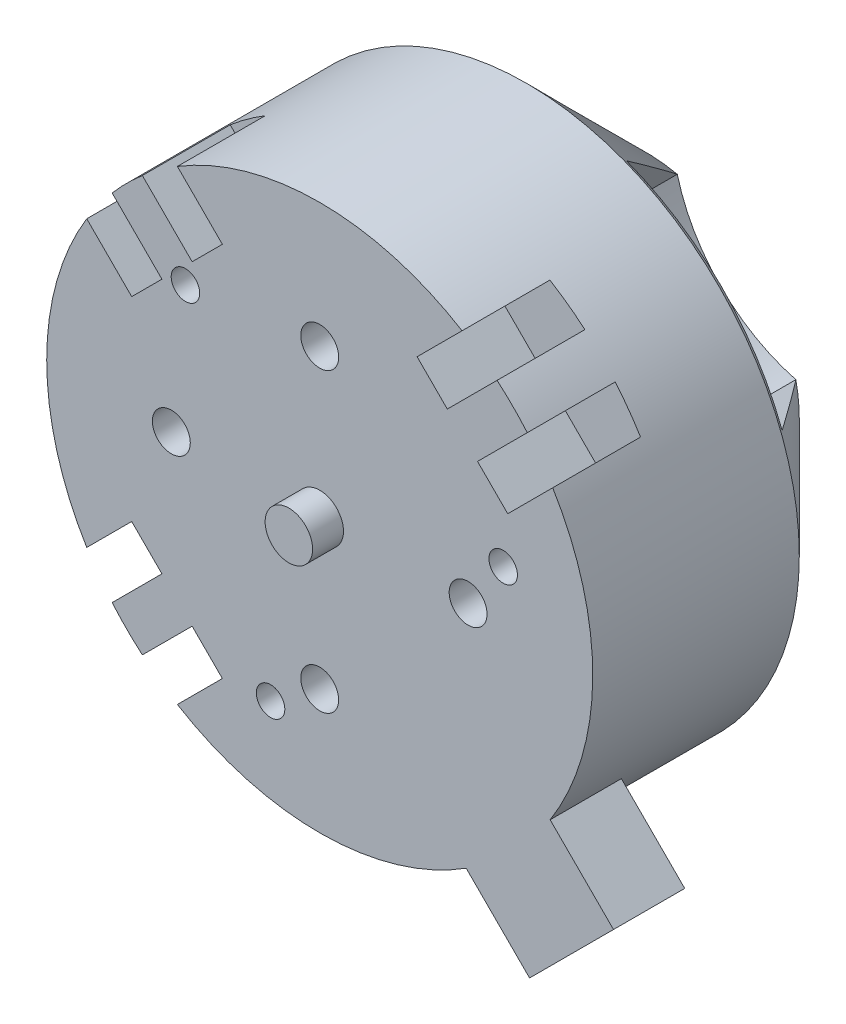
SolidWorks part; units mm, degrees
ref_plane "前视基准面" through (0, 0, 0) normal (0, 0, 1) x (1, 0, 0)
ref_plane "上视基准面" through (0, 0, 0) normal (0, 1, 0) x (1, 0, 0)
ref_plane "右视基准面" through (0, 0, 0) normal (1, 0, 0) x (0, 0, -1)
sketch "草图1" plane through (0, 0, 0) normal (0, 0, 1) x (1, 0, 0)
  circle A0 centre (0, 0) radius 23
extrude "凸台-拉伸1" add sketch "草图1" along normal blind 25
sketch "草图2" plane through (0, 0, 0) normal (0, 0, -1) x (-1, 0, 0)
  circle A0 centre (6, 0) radius 1.5
  circle A1 centre (0, -6) radius 1.5
  circle A2 centre (-6, 0) radius 1.5
  circle A3 centre (0, 6) radius 1.5
  circle A4 centre (0, 0) radius 2.6
  point P10 (0, 0)
extrude "切除-拉伸1" cut sketch "草图2" against normal blind 10
sketch "草图3" plane through (0, 0, 10) normal (0, 0, -1) x (-1, 0, 0)
  circle A1 centre (0, 0) radius 2.6
  circle A2 centre (0, 0) radius 2.6
  dimension "D1" = 0
extrude "凸台-拉伸2" add sketch "草图3" against normal offset from surface (27 mm away) 12 up to face at (23, 0, 25) offset beyond the face yes
chamfer "倒角1" distance 10 angle 45 1 edges at (23, 0, 0)
sketch "草图4" plane through (0, 0, 0) normal (0, 0, -1) x (-1, 0, 0)
  line L0 (2.7214, -12.712) -> (8.2046, -21.4869)
  line L1 (12.712, 2.7214) -> (21.4869, 8.2046)
  line L2 (2.7214, 12.712) -> (8.2046, 21.4869)
  line L3 (12.712, -2.7214) -> (21.4869, -8.2046)
  line L4 (-12.712, -2.7214) -> (-21.4869, -8.2046)
  line L5 (-2.7214, -12.712) -> (-8.2046, -21.4869)
  line L6 (-2.7214, 12.712) -> (-8.2046, 21.4869)
  line L7 (-12.712, 2.7214) -> (-21.4869, 8.2046)
  arc A0 (12.712, -2.7214) -> (2.7214, -12.712) centre (16.2635, -16.2635) ccw
  circle A1 centre (0, 0) radius 13 construction
  circle A2 centre (0, 0) radius 23 construction
  arc A3 (2.7214, 12.712) -> (12.712, 2.7214) centre (16.2635, 16.2635) ccw
  arc A4 (12.712, -2.7214) -> (-12.712, -2.7214) centre (0, 0) ccw
  arc A5 (21.4869, 8.2046) -> (8.2046, 21.4869) centre (0, 0) ccw
  arc A6 (12.712, -2.7214) -> (-12.712, -2.7214) centre (0, 0) ccw
  arc A7 (8.2046, -21.4869) -> (21.4869, -8.2046) centre (0, 0) ccw
  arc A8 (-2.7214, -12.712) -> (-12.712, -2.7214) centre (-16.2635, -16.2635) ccw
  arc A9 (12.712, -2.7214) -> (-12.712, -2.7214) centre (0, 0) ccw
  arc A10 (-21.4869, -8.2046) -> (-8.2046, -21.4869) centre (0, 0) ccw
  arc A11 (-12.712, 2.7214) -> (-2.7214, 12.712) centre (-16.2635, 16.2635) ccw
  arc A12 (12.712, -2.7214) -> (-12.712, -2.7214) centre (0, 0) ccw
  arc A13 (-8.2046, 21.4869) -> (-21.4869, 8.2046) centre (0, 0) ccw
  arc A14 (2.7214, -12.712) -> (3.8008, -12.432) centre (0, 0) ccw
  arc A15 (2.7214, -12.712) -> (3.8008, -12.432) centre (0, 0) ccw
  arc A16 (2.7214, -12.712) -> (3.8008, -12.432) centre (0, 0) ccw
  arc A17 (2.7214, -12.712) -> (3.8008, -12.432) centre (0, 0) ccw
  point P31 (0, 0)
  circle M12 centre (0, 0) radius 13
  dimension "D1" = 4
extrude "切除-拉伸2" cut sketch "草图4" against normal blind 9.5 contours L0 A7 L3 M12 | A0 M12 | A3 M12 | L1 A5 L2 M12 | L6 A13 L7 M12 | A11 M12 | L4 A10 L5 M12 | A8 M12
sketch "草图5" plane through (0, 0, 25) normal (0, 0, 1) x (1, 0, 0)
  circle A4 centre (0, 12.5) radius 1.5957
  circle A5 centre (12.5, 0) radius 1.5957
  circle A6 centre (0, -12.5) radius 1.5957
  circle A7 centre (-12.5, 0) radius 1.5957
  point P13 (-4.7872, 7.4468)
  point P15 (-4.7872, -7.4468)
  point P27 (0, 0)
  point P32 (0, 0)
  point P41 (0, 0)
extrude "切除-拉伸3" cut sketch "草图5" against normal blind 2
sketch "草图6" plane through (0, 0, 37) normal (0, 0, 1) x (1, 0, 0)
  circle A1 centre (0, 0) radius 2.6
  circle A2 centre (0, 0) radius 2.6
  dimension "D1" = 0
extrude "切除-拉伸4" cut sketch "草图6" against normal up to surface (12 mm away) up to face at (1.5957, 12.5, 25)
sketch "草图7" plane through (0, 0, 25) normal (0, 0, 1) x (1, 0, 0)
  circle A0 centre (0, 0) radius 2
extrude "凸台-拉伸3" add sketch "草图7" along normal blind 5
sketch "草图8" plane through (0, 0, 25) normal (0, 0, 1) x (1, 0, 0)
  line L1 (17.6777, -24.7487) -> (24.7487, -17.6777)
  line L2 (24.7487, -17.6777) -> (17.5976, -10.5265)
  line L3 (17.5976, -10.5265) -> (10.5265, -17.5976)
  line L4 (17.6777, -24.7487) -> (10.5265, -17.5976)
  point P7 (14.062, -14.062)
extrude "凸台-拉伸4" add sketch "草图8" against normal blind 5
sketch "草图9" plane through (0, 0, 25) normal (0, 0, 1) x (1, 0, 0)
  line L0 (10.748, 13.2936) -> (14.9408, 17.4864)
  line L1 (-13.2936, 10.748) -> (-17.4864, 14.9408)
  line L2 (-10.748, 13.2936) -> (-8.2024, 15.8392)
  line L3 (-10.748, 13.2936) -> (-14.7902, 17.3358)
  line L4 (-8.2024, 15.8392) -> (-10.748, 13.2936)
  line L5 (-8.2024, 15.8392) -> (-11.9905, 19.6272)
  line L6 (-15.8392, 8.2024) -> (-19.6272, 11.9905)
  line L7 (-8.2024, 15.8392) -> (-10.748, 13.2936)
  line L8 (-8.2024, 15.8392) -> (-11.9905, 19.6272)
  line L9 (-10.748, 13.2936) -> (-14.9408, 17.4864)
  line L10 (-15.8392, 8.2024) -> (-13.2936, 10.748)
  line L11 (-15.8392, 8.2024) -> (-19.6272, 11.9905)
  line L12 (-15.8392, 8.2024) -> (-13.2936, 10.748)
  line L13 (-13.2936, 10.748) -> (-17.3358, 14.7902)
  line L14 (-13.2936, 10.748) -> (-15.8392, 8.2024)
  line L15 (13.2936, 10.748) -> (15.8392, 8.2024)
  line L16 (13.2936, 10.748) -> (17.3358, 14.7902)
  line L17 (15.8392, 8.2024) -> (13.2936, 10.748)
  line L18 (15.8392, 8.2024) -> (19.6272, 11.9905)
  line L19 (8.2024, 15.8392) -> (11.9905, 19.6272)
  line L20 (15.8392, 8.2024) -> (13.2936, 10.748)
  line L21 (15.8392, 8.2024) -> (19.6272, 11.9905)
  line L22 (13.2936, 10.748) -> (17.4864, 14.9408)
  line L23 (8.2024, 15.8392) -> (10.748, 13.2936)
  line L24 (8.2024, 15.8392) -> (11.9905, 19.6272)
  line L25 (8.2024, 15.8392) -> (10.748, 13.2936)
  line L26 (10.748, 13.2936) -> (14.7902, 17.3358)
  line L27 (10.748, 13.2936) -> (8.2024, 15.8392)
  line L28 (-10.748, -13.2936) -> (-14.9408, -17.4864)
  line L29 (-13.2936, -10.748) -> (-15.8392, -8.2024)
  line L30 (-13.2936, -10.748) -> (-17.3358, -14.7902)
  line L31 (-15.8392, -8.2024) -> (-13.2936, -10.748)
  line L32 (-15.8392, -8.2024) -> (-19.6272, -11.9905)
  line L33 (-8.2024, -15.8392) -> (-11.9905, -19.6272)
  line L34 (-15.8392, -8.2024) -> (-13.2936, -10.748)
  line L35 (-15.8392, -8.2024) -> (-19.6272, -11.9905)
  line L36 (-13.2936, -10.748) -> (-17.4864, -14.9408)
  line L37 (-8.2024, -15.8392) -> (-10.748, -13.2936)
  line L38 (-8.2024, -15.8392) -> (-11.9905, -19.6272)
  line L39 (-8.2024, -15.8392) -> (-10.748, -13.2936)
  line L40 (-10.748, -13.2936) -> (-14.7902, -17.3358)
  line L41 (-10.748, -13.2936) -> (-8.2024, -15.8392)
  arc A1 (19.41, -12.339) -> (12.339, -19.41) centre (0, 0) ccw construction
  arc A2 (19.41, -12.339) -> (12.339, -19.41) centre (0, 0) ccw
  point P38 (0, 0)
  arc M1 (19.41, -12.339) -> (12.339, -19.41) centre (0, 0) ccw
extrude "切除-拉伸5" cut sketch "草图9" against normal blind 5 contours L6 L10 L1 M1 | L9 L3 L2 L5 M1 | L19 L23 L0 M1 | L22 L16 L15 L18 M1 | L33 L37 L28 M1 | L36 L30 L29 L32 M1
sketch "草图10" plane through (0, 0, 25) normal (0, 0, 1) x (1, 0, 0)
  line L21 (-10.748, -13.2936) -> (-8.2024, -15.8392)
  line L22 (-8.2024, -15.8392) -> (-11.9905, -19.6272)
  line L23 (12.339, -19.41) -> (17.6777, -24.7487)
  line L24 (17.6777, -24.7487) -> (24.7487, -17.6777)
  line L25 (24.7487, -17.6777) -> (19.41, -12.339)
  line L26 (19.6272, 11.9905) -> (15.8392, 8.2024)
  line L27 (15.8392, 8.2024) -> (13.2936, 10.748)
  line L28 (13.2936, 10.748) -> (17.4864, 14.9408)
  line L29 (14.9408, 17.4864) -> (10.748, 13.2936)
  line L30 (10.748, 13.2936) -> (8.2024, 15.8392)
  line L31 (8.2024, 15.8392) -> (11.9905, 19.6272)
  line L32 (-11.9905, 19.6272) -> (-8.2024, 15.8392)
  line L33 (-8.2024, 15.8392) -> (-10.748, 13.2936)
  line L34 (-10.748, 13.2936) -> (-14.9408, 17.4864)
  line L35 (-17.4864, 14.9408) -> (-13.2936, 10.748)
  line L36 (-13.2936, 10.748) -> (-15.8392, 8.2024)
  line L37 (-15.8392, 8.2024) -> (-19.6272, 11.9905)
  line L38 (-19.6272, -11.9905) -> (-15.8392, -8.2024)
  line L39 (-15.8392, -8.2024) -> (-13.2936, -10.748)
  line L40 (-13.2936, -10.748) -> (-17.4864, -14.9408)
  line L41 (-14.9408, -17.4864) -> (-10.748, -13.2936)
  line L42 (-10.748, -13.2936) -> (-8.2024, -15.8392)
  line L43 (-8.2024, -15.8392) -> (-11.9905, -19.6272)
  line L44 (12.339, -19.41) -> (17.6777, -24.7487)
  line L45 (17.6777, -24.7487) -> (24.7487, -17.6777)
  line L46 (24.7487, -17.6777) -> (19.41, -12.339)
  line L47 (19.6272, 11.9905) -> (15.8392, 8.2024)
  line L48 (15.8392, 8.2024) -> (13.2936, 10.748)
  line L49 (13.2936, 10.748) -> (17.4864, 14.9408)
  line L50 (14.9408, 17.4864) -> (10.748, 13.2936)
  line L51 (10.748, 13.2936) -> (8.2024, 15.8392)
  line L52 (8.2024, 15.8392) -> (11.9905, 19.6272)
  line L53 (-11.9905, 19.6272) -> (-8.2024, 15.8392)
  line L54 (-8.2024, 15.8392) -> (-10.748, 13.2936)
  line L55 (-10.748, 13.2936) -> (-14.9408, 17.4864)
  line L56 (-17.4864, 14.9408) -> (-13.2936, 10.748)
  line L57 (-13.2936, 10.748) -> (-15.8392, 8.2024)
  line L58 (-15.8392, 8.2024) -> (-19.6272, 11.9905)
  line L59 (-19.6272, -11.9905) -> (-15.8392, -8.2024)
  line L60 (-15.8392, -8.2024) -> (-13.2936, -10.748)
  line L61 (-13.2936, -10.748) -> (-17.4864, -14.9408)
  line L62 (-14.9408, -17.4864) -> (-10.748, -13.2936)
  circle A0 centre (0, 12.5) radius 1.5957 construction
  circle A1 centre (-12.5, 0) radius 1.5957 construction
  circle A2 centre (0, -12.5) radius 1.5957 construction
  circle A3 centre (12.5, 0) radius 1.5957 construction
  circle A4 centre (0, 12.5) radius 1.5957
  circle A5 centre (-12.5, 0) radius 1.5957
  circle A6 centre (0, -12.5) radius 1.5957
  arc A7 (-11.9905, -19.6272) -> (12.339, -19.41) centre (0, 0) ccw
  arc A8 (19.41, -12.339) -> (19.6272, 11.9905) centre (0, 0) ccw
  arc A9 (17.4864, 14.9408) -> (14.9408, 17.4864) centre (0, 0) ccw
  arc A10 (11.9905, 19.6272) -> (-11.9905, 19.6272) centre (0, 0) ccw
  arc A11 (-14.9408, 17.4864) -> (-17.4864, 14.9408) centre (0, 0) ccw
  arc A12 (-19.6272, 11.9905) -> (-19.6272, -11.9905) centre (0, 0) ccw
  arc A13 (-17.4864, -14.9408) -> (-14.9408, -17.4864) centre (0, 0) ccw
  arc A14 (-11.9905, -19.6272) -> (12.339, -19.41) centre (0, 0) ccw
  arc A15 (19.41, -12.339) -> (19.6272, 11.9905) centre (0, 0) ccw
  arc A16 (17.4864, 14.9408) -> (14.9408, 17.4864) centre (0, 0) ccw
  arc A17 (11.9905, 19.6272) -> (-11.9905, 19.6272) centre (0, 0) ccw
  arc A18 (-14.9408, 17.4864) -> (-17.4864, 14.9408) centre (0, 0) ccw
  arc A19 (-19.6272, 11.9905) -> (-19.6272, -11.9905) centre (0, 0) ccw
  arc A20 (-17.4864, -14.9408) -> (-14.9408, -17.4864) centre (0, 0) ccw
  circle A21 centre (12.5, 0) radius 1.5957
  dimension "D1" = 0
extrude "凸台-拉伸5" add sketch "草图10" along normal blind 2.4
sketch "草图11" plane through (0, 0, 20) normal (0, 0, -1) x (-1, 0, 0)
  line L3 (-17.6777, -24.7487) -> (-12.339, -19.41)
  line L4 (-19.41, -12.339) -> (-24.7487, -17.6777)
  line L5 (-24.7487, -17.6777) -> (-17.6777, -24.7487)
  line L6 (-17.6777, -24.7487) -> (-12.339, -19.41)
  line L7 (-19.41, -12.339) -> (-24.7487, -17.6777)
  line L8 (-24.7487, -17.6777) -> (-17.6777, -24.7487)
  arc A1 (-19.41, -12.339) -> (-12.339, -19.41) centre (0, 0) ccw
  arc A2 (-19.41, -12.339) -> (-12.339, -19.41) centre (0, 0) ccw
  dimension "D1" = 0
extrude "切除-拉伸6" cut sketch "草图11" against normal blind 1.4
sketch "草图12" plane through (0, 0, 27.4) normal (0, 0, 1) x (1, 0, 0)
  circle A0 centre (15.4548, 4.1411) radius 1.2
  circle A1 centre (-4.1411, -15.4548) radius 1.2
  circle A2 centre (-11.3137, 11.3137) radius 1.2
  point P6 (0, 0)
extrude "切除-拉伸7" cut sketch "草图12" against normal blind 5
